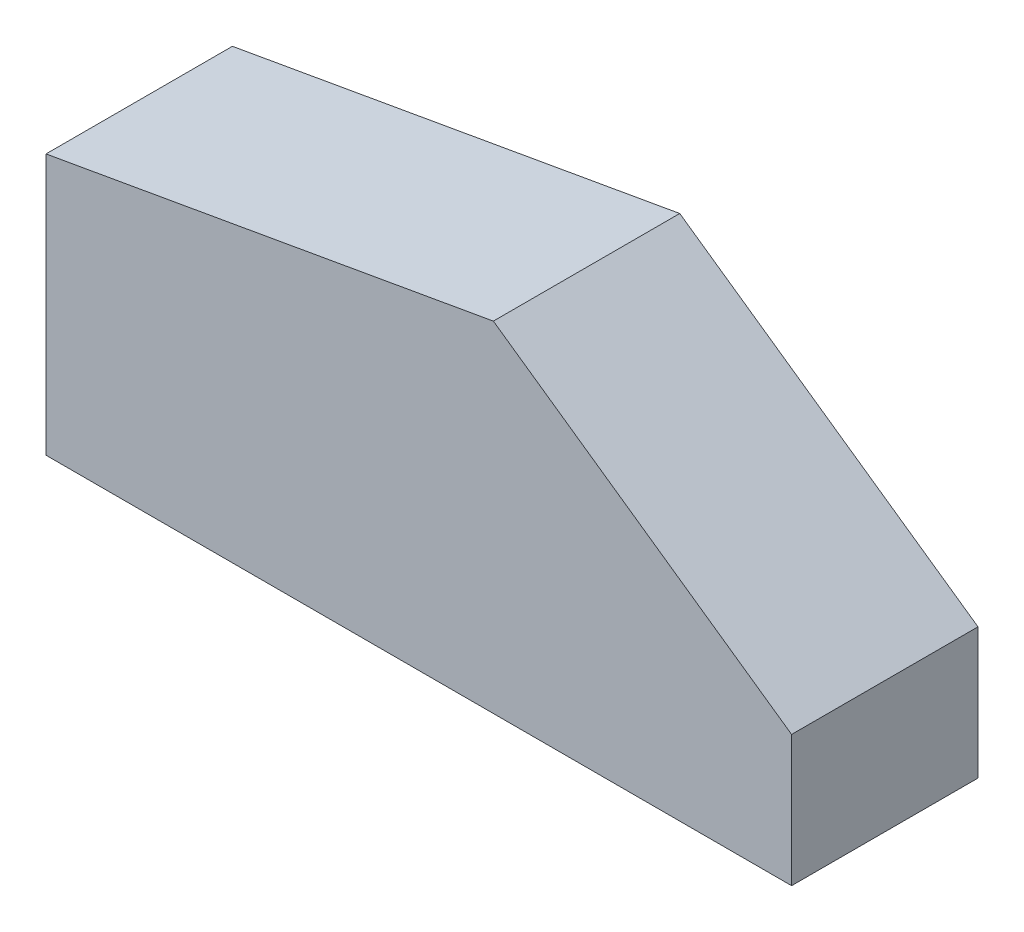
SolidWorks part; units mm, degrees
ref_plane "Front Plane" through (0, 0, 0) normal (0, 0, 1) x (1, 0, 0)
ref_plane "Top Plane" through (0, 0, 0) normal (0, 1, 0) x (1, 0, 0)
ref_plane "Right Plane" through (0, 0, 0) normal (1, 0, 0) x (0, 0, -1)
sketch "Sketch1" plane through (0, 0, 0) normal (0, 0, 1) x (1, 0, 0)
  line L0 (0, 0) -> (100, 0)
  line L1 (100, 0) -> (100, 17.5713)
  line L2 (100, 17.5713) -> (60, 45.5796)
  line L3 (60, 45.5796) -> (0, 35)
  line L4 (0, 35) -> (0, 0)
  dimension "D1" = 135
  dimension "D2" = 100
  dimension "D3" = 35
  dimension "D4" = 60
  dimension "D5" = 100
extrude "Boss-Extrude1" add sketch "Sketch1" along normal blind 25
